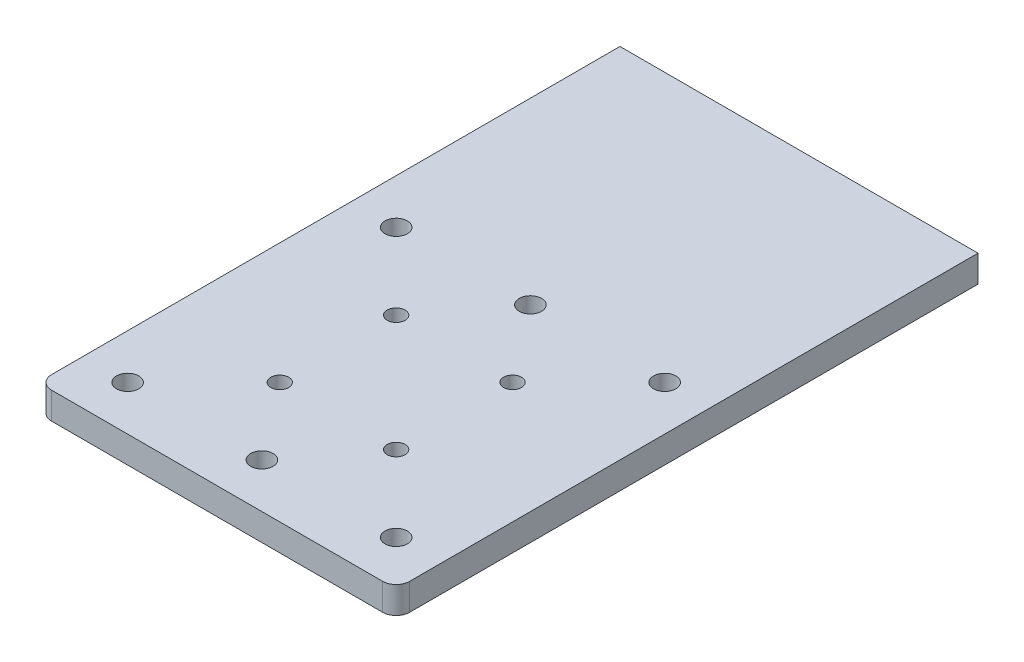
SolidWorks part; units mm, degrees
ref_plane "Front Plane" through (0, 0, 0) normal (0, 0, 1) x (1, 0, 0)
ref_plane "Top Plane" through (0, 0, 0) normal (0, 1, 0) x (1, 0, 0)
ref_plane "Right Plane" through (0, 0, 0) normal (1, 0, 0) x (0, 0, -1)
sketch "Sketch1" plane through (0, 0, 0) normal (0, 1, 0) x (1, 0, 0)
  line L1 (0, 0) -> (26, 0) construction
  line L2 (0, 0) -> (0, 26) construction
  line L3 (0, 26) -> (26, 26) construction
  line L4 (26, 0) -> (26, 26) construction
  line L5 (-27, 103) -> (53, 103)
  line L6 (-27, 103) -> (-27, -27)
  line L7 (-27, -27) -> (53, -27)
  line L8 (53, 103) -> (53, -27)
  line L10 (0, 26) -> (26, 0) construction
  line L11 (0, 0) -> (26, 26) construction
  circle A0 centre (0, 26) radius 2
  circle A1 centre (26, 26) radius 2
  circle A2 centre (26, 0) radius 2
  circle A3 centre (0, 0) radius 2
  circle A4 centre (-17, 43) radius 2.5
  circle A5 centre (43, 43) radius 2.5
  circle A6 centre (43, -17) radius 2.5
  circle A7 centre (-17, -17) radius 2.5
  circle A8 centre (13, 43) radius 2.5
  circle A9 centre (13, -17) radius 2.5
  point P14 (13, 13)
  point P15 (13, 13)
  dimension "D1" = 26
  dimension "D2" = 4
  dimension "D3" = 4
  dimension "D4" = 4
  dimension "D5" = 4
  dimension "D8" = 5
  dimension "D9" = 60
  dimension "D10" = 5
  dimension "D11" = 5
  dimension "D12" = 5
  dimension "D13" = 10
  dimension "D14" = 5
  dimension "D15" = 5
  dimension "D6" = 130
  dimension "D7" = 80
extrude "Boss-Extrude1" add sketch "Sketch1" along normal blind 6
fillet "Fillet1" radius 3 2 edges at (53, 3, 27) (-27, 3, 27)
